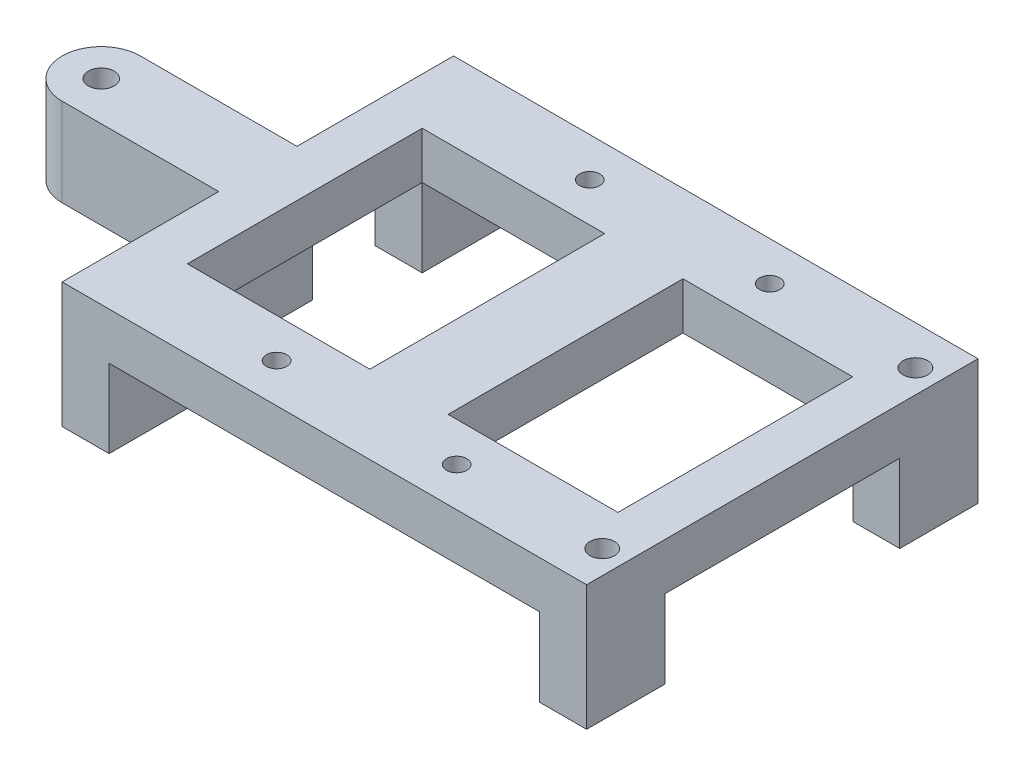
SolidWorks part; units mm, degrees
ref_plane "Front Plane" through (0, 0, 0) normal (0, 0, 1) x (1, 0, 0)
ref_plane "Top Plane" through (0, 0, 0) normal (0, 1, 0) x (1, 0, 0)
ref_plane "Right Plane" through (0, 0, 0) normal (1, 0, 0) x (0, 0, -1)
sketch "Sketch1" plane through (0, 0, 0) normal (0, 0, 1) x (1, 0, 0)
  line L0 (-42.545, -20.32) -> (42.545, -20.32)
  line L1 (-34.925, -12.7) -> (34.925, -12.7)
  line L2 (-34.925, -12.7) -> (-34.925, 12.7)
  line L3 (-34.925, 12.7) -> (34.925, 12.7)
  line L4 (34.925, -12.7) -> (34.925, 12.7)
  line L5 (-34.925, -12.7) -> (34.925, 12.7) construction
  line L6 (-34.925, 12.7) -> (34.925, -12.7) construction
  line L7 (42.545, -20.32) -> (42.545, 20.32)
  line L8 (-42.545, 20.32) -> (42.545, 20.32)
  line L9 (-42.545, -20.32) -> (-42.545, 20.32)
  point P0 (0, 0)
  dimension "D1" = 69.85
  dimension "D2" = 25.4
  dimension "D3" = 7.62
extrude "Boss-Extrude1" add sketch "Sketch1" against normal blind 12.7
sketch "Sketch2" plane through (0, 0, -12.7) normal (0, 0, -1) x (-1, 0, 0)
  line L0 (-34.925, 12.7) -> (34.925, 12.7) construction
  line L1 (-42.545, 20.32) -> (-34.925, 20.32)
  line L2 (-42.545, 20.32) -> (-42.545, 12.7)
  line L3 (-42.545, 12.7) -> (-34.925, 12.7)
  line L4 (-34.925, 20.32) -> (-34.925, 12.7)
  line L5 (-7.3765, 12.7) -> (-7.3765, 20.32)
  line L6 (-7.3765, 12.7) -> (5.3235, 12.7)
  line L7 (-7.3765, 20.32) -> (5.3235, 20.32)
  line L8 (5.3235, 12.7) -> (5.3235, 20.32)
  line L9 (-7.3765, 12.7) -> (5.3235, 20.32) construction
  line L10 (-7.3765, 20.32) -> (5.3235, 12.7) construction
  line L11 (-30.48, 0) -> (46.0926, 0) construction
  line L12 (42.545, 20.32) -> (34.925, 20.32)
  line L13 (42.545, 20.32) -> (42.545, 12.7)
  line L14 (42.545, 12.7) -> (34.925, 12.7)
  line L15 (34.925, 20.32) -> (34.925, 12.7)
  line L16 (-42.545, 20.32) -> (42.545, 20.32) construction
  line L17 (-7.3765, -20.32) -> (5.3235, -12.7) construction
  line L18 (-7.3765, -12.7) -> (5.3235, -20.32) construction
  line L19 (34.925, -20.32) -> (34.925, -12.7)
  line L20 (42.545, -12.7) -> (34.925, -12.7)
  line L21 (42.545, -20.32) -> (42.545, -12.7)
  line L22 (42.545, -20.32) -> (34.925, -20.32)
  line L23 (5.3235, -12.7) -> (5.3235, -20.32)
  line L24 (-7.3765, -20.32) -> (5.3235, -20.32)
  line L25 (-7.3765, -12.7) -> (5.3235, -12.7)
  line L26 (-7.3765, -12.7) -> (-7.3765, -20.32)
  line L27 (-34.925, -20.32) -> (-34.925, -12.7)
  line L28 (-42.545, -12.7) -> (-34.925, -12.7)
  line L29 (-42.545, -20.32) -> (-42.545, -12.7)
  line L30 (-42.545, -20.32) -> (-34.925, -20.32)
  point P8 (-1.0265, 16.51)
  point P32 (-1.0265, -16.51)
  dimension "D1" = 7.62
  dimension "D2" = 12.7
  dimension "D3" = 7.62
extrude "Boss-Extrude2" add sketch "Sketch2" along normal blind 38.1
sketch "Sketch4" plane through (0, 0, -50.8) normal (0, 0, -1) x (-1, 0, 0)
  line L1 (-42.545, 20.32) -> (42.545, 20.32)
  line L2 (-42.545, 20.32) -> (-42.545, -20.32)
  line L3 (-42.545, -20.32) -> (42.545, -20.32)
  line L4 (42.545, 20.32) -> (42.545, -20.32)
  line L5 (-34.925, 12.7) -> (34.925, 12.7)
  line L6 (-34.925, 12.7) -> (-34.925, -12.7)
  line L7 (-34.925, -12.7) -> (34.925, -12.7)
  line L8 (34.925, 12.7) -> (34.925, -12.7)
extrude "Boss-Extrude3" add sketch "Sketch4" along normal blind 12.7
sketch "Sketch5" plane through (0, 20.32, 0) normal (0, 1, 0) x (1, 0, 0)
  line L0 (34.925, 12.7) -> (42.545, 12.7) construction
  line L1 (42.545, 63.5) -> (42.545, 0) construction
  line L2 (42.545, 12.7) -> (42.545, 0) construction
  line L3 (-42.545, 31.75) -> (42.545, 31.75) construction
  line L5 (-42.545, 63.5) -> (-42.545, 0) construction
  circle A0 centre (-14.1017, 6.35) radius 1.9939
  circle A1 centre (15.1083, 6.35) radius 1.9939
  circle A2 centre (15.1083, 57.15) radius 1.9939
  circle A3 centre (-14.1017, 57.15) radius 1.9939
  point P21 (-14.1017, 6.35)
  point P22 (15.1083, 6.35)
  dimension "D1" = 3.9878
  dimension "D2" = 3.9878
sketch "Sketch6" plane through (-42.545, 0, 0) normal (-1, 0, 0) x (0, 0, 1)
  line L0 (-63.5, 20.32) -> (0, 20.32) construction
  line L1 (-38.1, 20.32) -> (-25.4, 20.32)
  line L2 (-38.1, 20.32) -> (-38.1, -20.32)
  line L3 (-38.1, -20.32) -> (-25.4, -20.32)
  line L4 (-25.4, 20.32) -> (-25.4, -20.32)
  line L5 (-63.5, -20.32) -> (0, -20.32) construction
  line L7 (-50.8, -12.7) -> (-50.8, 12.7) construction
  dimension "D1" = 12.7
  dimension "D2" = 12.7
extrude "Boss-Extrude4" add sketch "Sketch6" against normal blind 2.54
sketch "Sketch7" plane through (-42.545, 0, 0) normal (-1, 0, 0) x (0, 0, 1)
  line L0 (-25.4, -12.7) -> (-25.4, 12.7) construction
  line L3 (-38.1, 11.1125) -> (-25.4, 11.1125)
  line L4 (-38.1, 11.1125) -> (-38.1, 6.0325)
  line L5 (-38.1, 6.0325) -> (-25.4, 6.0325)
  line L6 (-25.4, 11.1125) -> (-25.4, 6.0325)
  line L8 (-38.1, -11.1125) -> (-25.4, -11.1125)
  line L9 (-38.1, -11.1125) -> (-38.1, -6.0325)
  line L10 (-38.1, -6.0325) -> (-25.4, -6.0325)
  line L11 (-25.4, -11.1125) -> (-25.4, -6.0325)
  dimension "D1" = 5.08
extrude "Boss-Extrude5" add sketch "Sketch7" along normal blind 25.4
sketch "Sketch8" plane through (-67.945, 0, 0) normal (-1, 0, 0) x (0, 0, 1)
  line L0 (-31.75, 11.1125) -> (-31.75, -11.1125) construction
  line L1 (-25.4, 11.1125) -> (-38.1, 11.1125) construction
  line L2 (-38.1, -11.1125) -> (-25.4, -11.1125) construction
  line L4 (-31.75, 11.1125) -> (-25.4, 11.1125)
  line L5 (-31.75, 11.1125) -> (-31.75, 6.0325)
  line L6 (-31.75, 6.0325) -> (-25.4, 6.0325)
  line L7 (-25.4, 11.1125) -> (-25.4, 6.0325)
  line L8 (-25.4, -11.1125) -> (-31.75, -11.1125)
  line L9 (-25.4, -11.1125) -> (-25.4, -6.0325)
  line L10 (-25.4, -6.0325) -> (-31.75, -6.0325)
  line L11 (-31.75, -11.1125) -> (-31.75, -6.0325)
  dimension "D1" = 5.08
revolve "Revolve2" add sketch "Sketch8" angle 180 about L0
sketch "Sketch10" plane through (0, 11.1125, 0) normal (0, 1, 0) x (1, 0, 0)
  line L0 (-67.945, 38.1) -> (-67.945, 25.4) construction
  line L1 (-74.295, 31.75) -> (-67.945, 31.75) construction
  arc A0 (-67.945, 38.1) -> (-67.945, 25.4) centre (-67.945, 31.75) ccw construction
  circle A1 centre (-67.945, 31.75) radius 2.0955
  dimension "D1" = 4.191
extrude "Cut-Extrude4" cut sketch "Sketch10" against normal through all
hole_wizard "M4x0.7 Tapped Hole1" positions "Sketch16" profile "Sketch15" tap size "M4x0.7" standard "ANSI Metric" end condition through all
sketch "Sketch16" plane through (0, 20.32, 0) normal (0, 1, 0) x (1, 0, 0)
  point P0 (-14.1017, 57.15)
  point P3 (15.1083, 57.15)
  point P6 (15.1083, 6.35)
  point P9 (-14.1017, 6.35)
sketch "Sketch15" plane through (-14.1017, 20.32, -57.15) normal (1, 0, 0) x (0, 0, 1)
  line L0 (0, 0) -> (0, 40.64)
  line L1 (0, 40.64) -> (1.65, 40.64)
  line L2 (1.65, 40.64) -> (1.65, 0)
  line L5 (1.65, 0) -> (0, 0)
  line L11 (0, -6.35) -> (0, 107.95) construction
  dimension "Thru Tap Drill Dia." = 3.3
  dimension "Thru Tap Drill Depth" = 40.64
cosmetic thread "Hole Thread1" parameters "D2"=4
cosmetic thread "Hole Thread2" parameters "D2"=4
cosmetic thread "Hole Thread3" parameters "D2"=4
cosmetic thread "Hole Thread4" parameters "D2"=4
sketch "Sketch17" plane through (0, 11.1125, 0) normal (0, 1, 0) x (1, 0, 0)
  line L0 (-67.945, 25.4) -> (-42.545, 25.4) construction
  line L1 (-67.945, 38.1) -> (-42.545, 38.1) construction
  line L2 (-42.545, 25.4) -> (-42.545, 38.1) construction
  line L3 (-67.945, 25.4) -> (-42.545, 25.4)
  line L4 (-67.945, 38.1) -> (-42.545, 38.1)
  line L5 (-42.545, 25.4) -> (-42.545, 38.1)
  arc A0 (-67.945, 38.1) -> (-67.945, 25.4) centre (-67.945, 31.75) ccw construction
  circle A1 centre (-67.945, 31.75) radius 2.0955 construction
  arc A2 (-67.945, 38.1) -> (-67.945, 25.4) centre (-67.945, 31.75) ccw
  circle A3 centre (-67.945, 31.75) radius 2.0955
extrude "Boss-Extrude6" add sketch "Sketch17" along normal up to surface (9.2075 mm away) up to face at (-14.1017, 20.32, -55.5)
sketch "Sketch18" plane through (0, -11.1125, 0) normal (0, -1, 0) x (1, 0, 0)
  line L0 (-42.545, -38.1) -> (-42.545, -25.4) construction
  line L1 (-67.945, -38.1) -> (-42.545, -38.1) construction
  line L2 (-67.945, -25.4) -> (-42.545, -25.4) construction
  line L3 (-42.545, -38.1) -> (-42.545, -25.4)
  line L4 (-67.945, -38.1) -> (-42.545, -38.1)
  line L5 (-67.945, -25.4) -> (-42.545, -25.4)
  arc A0 (-67.945, -25.4) -> (-67.945, -38.1) centre (-67.945, -31.75) ccw construction
  circle A1 centre (-67.945, -31.75) radius 2.0955 construction
  arc A2 (-67.945, -25.4) -> (-67.945, -38.1) centre (-67.945, -31.75) ccw
  circle A3 centre (-67.945, -31.75) radius 2.0955
extrude "Boss-Extrude7" add sketch "Sketch18" along normal blind 6.35
sketch "Sketch19" plane through (-42.545, 0, 0) normal (-1, 0, 0) x (0, 0, 1)
  line L0 (-63.5, 0) -> (0, 0) construction
  line L1 (-63.5, -20.32) -> (-63.5, 20.32) construction
sketch "Sketch24" plane through (-42.545, 0, 0) normal (-1, 0, 0) x (0, 0, 1)
  line L1 (-63.5, 0) -> (0, 0)
  line L2 (-63.5, 0) -> (-63.5, -20.32)
  line L3 (-63.5, -20.32) -> (0, -20.32)
  line L4 (0, 0) -> (0, -20.32)
extrude "Cut-Extrude9" cut sketch "Sketch24" against normal through all and the other way through all
sketch "Sketch25" plane through (0, 20.32, 0) normal (0, 1, 0) x (1, 0, 0)
  line L0 (34.925, 50.8) -> (34.925, 63.5) construction
  line L1 (34.925, 12.7) -> (34.925, 0) construction
  line L2 (34.925, 6.35) -> (42.545, 6.35) construction
  line L3 (42.545, 12.7) -> (42.545, 0) construction
  line L4 (34.925, 57.15) -> (42.545, 57.15) construction
  line L5 (42.545, 63.5) -> (42.545, 0) construction
  circle A0 centre (38.735, 57.15) radius 2
  circle A1 centre (38.735, 6.35) radius 2
  dimension "D1" = 4
  dimension "D2" = 4
extrude "Cut-Extrude10" cut sketch "Sketch25" against normal up to next
